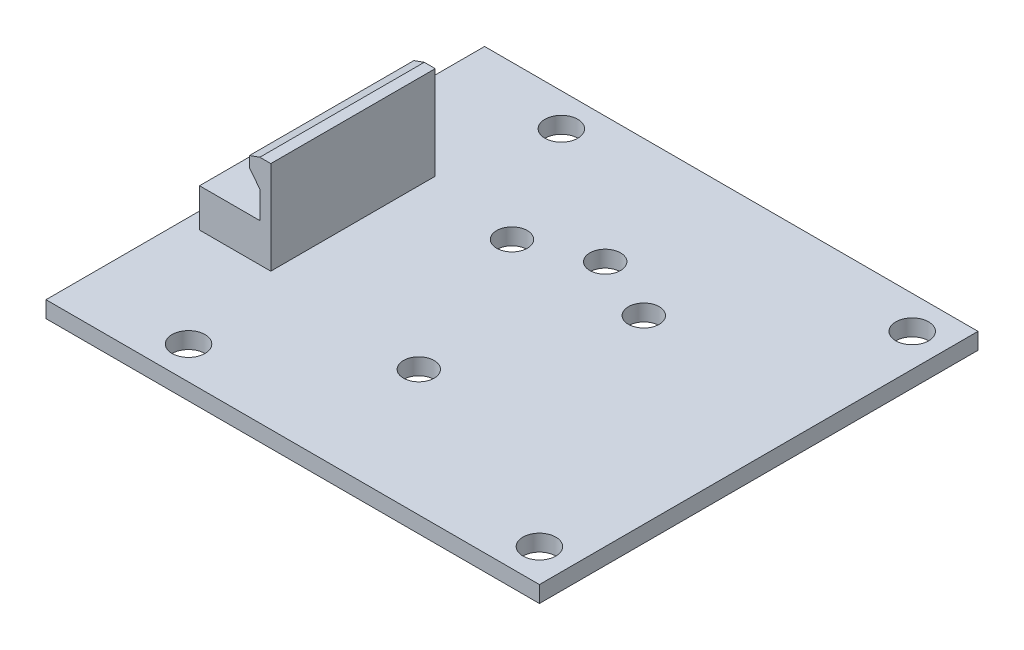
SolidWorks part; units mm, degrees
ref_plane "Front Plane" through (0, 0, 0) normal (0, 0, 1) x (1, 0, 0)
ref_plane "Top Plane" through (0, 0, 0) normal (0, 1, 0) x (1, 0, 0)
ref_plane "Right Plane" through (0, 0, 0) normal (1, 0, 0) x (0, 0, -1)
sketch "Sketch2" plane through (0, 0, 0) normal (0, 1, 0) x (1, 0, 0)
  line L1 (-22.5, 20) -> (22.5, 20)
  line L2 (-22.5, 20) -> (-22.5, -20)
  line L3 (-22.5, -20) -> (22.5, -20)
  line L4 (22.5, 20) -> (22.5, -20)
  line L5 (-22.5, 20) -> (22.5, -20) construction
  line L6 (-22.5, -20) -> (22.5, 20) construction
  point P0 (0, 0)
  dimension "D1" = 40
  dimension "D2" = 45
extrude "Boss-Extrude2" add sketch "Sketch2" against normal blind 1.5
sketch "Sketch4" plane through (0, 0, 0) normal (0, 1, 0) x (1, 0, 0)
  line L0 (0, 0) -> (0, 8.5) construction
  line L1 (0, 0) -> (6.0104, 6.0104) construction
  circle A0 centre (0, 0) radius 8.5 construction
  circle A1 centre (0, 8.5) radius 1.4
  circle A2 centre (6.0104, 6.0104) radius 1.4
  circle A3 centre (8.5, 0) radius 1.4 [skipped]
  circle A4 centre (6.0104, -6.0104) radius 1.4 [skipped]
  circle A5 centre (0, -8.5) radius 1.4
  circle A6 centre (-6.0104, -6.0104) radius 1.4 [skipped]
  circle A7 centre (-8.5, 0) radius 1.4 [skipped]
  circle A8 centre (-6.0104, 6.0104) radius 1.4
  dimension "D1" = 8
  dimension "D2" = 45
extrude "Cut-Extrude1" cut sketch "Sketch4" against normal through all
sketch "Sketch5" plane through (0, 0, 0) normal (0, 1, 0) x (1, 0, 0)
  line L0 (-22.5, 20) -> (-22.5, -20) construction
  line L1 (-21, -7.5) -> (-14.5, -7.5)
  line L2 (-21, -7.5) -> (-21, 7.5)
  line L3 (-21, 7.5) -> (-14.5, 7.5)
  line L4 (-14.5, -7.5) -> (-14.5, 7.5)
  line L5 (22.5, 20) -> (-22.5, 20) construction
  dimension "D1" = 15
  dimension "D2" = 1.5
  dimension "D3" = 6.5
  dimension "D4" = 12.5
extrude "Boss-Extrude3" add sketch "Sketch5" along normal blind 3.5
ref_plane "Plane1" through (0, 3.5, 0) normal (0, 1, 0) x (1, 0, 0)
sketch "Sketch6" plane through (0, 3.5, 0) normal (0, 1, 0) x (1, 0, 0)
  line L0 (-14.5, 7.5) -> (-21, 7.5) construction
  line L1 (-14.5, -7.5) -> (-15.5, -7.5)
  line L2 (-14.5, -7.5) -> (-14.5, 7.5)
  line L3 (-14.5, 7.5) -> (-15.5, 7.5)
  line L4 (-15.5, -7.5) -> (-15.5, 7.5)
  dimension "D1" = 1
extrude "Boss-Extrude4" add sketch "Sketch6" along normal blind 5
ref_plane "Plane2" through (0, 0, 7.5) normal (0, 0, 1) x (1, 0, 0)
sketch "Sketch7" plane through (0, 0, 7.5) normal (0, 0, 1) x (1, 0, 0)
  line L0 (-15.5, 8.5) -> (-16.4428, 8.1667)
  line L1 (-16.4428, 8.1667) -> (-16.4428, 7.1667)
  line L2 (-16.4428, 7.1667) -> (-15.5, 6)
  line L3 (-15.5, 8.5) -> (-15.5, 3.5) construction
  line L10 (-21, 0) -> (-14.5, 0)
  line L11 (-14.5, 0) -> (-14.5, 8.5)
  line L12 (-14.5, 8.5) -> (-15.5, 8.5)
  line L13 (-15.5, 8.5) -> (-15.5, 3.5)
  line L14 (-15.5, 3.5) -> (-21, 3.5)
  line L15 (-21, 3.5) -> (-21, 0)
  line L19 (-15.5, 8.5) -> (-15.5, 6)
  dimension "D1" = 1
  dimension "D2" = 1
  dimension "D3" = 1.5
  dimension "D4" = 0
extrude "Boss-Extrude5" add sketch "Sketch7" against normal blind 15
sketch "Sketch9" plane through (0, 0, 0) normal (0, 1, 0) x (1, 0, 0)
  line L0 (-22.5, 20) -> (-22.5, -20) construction
  line L1 (22.5, 20) -> (-22.5, 20) construction
  line L2 (-22.5, -20) -> (22.5, -20) construction
  line L3 (22.5, -20) -> (22.5, 20) construction
  circle A0 centre (-12.5, 17) radius 1.5
  circle A1 centre (-12.5, -17) radius 1.5
  circle A2 centre (19.5, 17) radius 1.5
  circle A3 centre (19.5, -17) radius 1.5
  dimension "D1" = 10
  dimension "D3" = 3
  dimension "D5" = 3
  dimension "D7" = 3
  dimension "D2" = 3
  dimension "D4" = 10
  dimension "D6" = 3
extrude "Cut-Extrude2" cut sketch "Sketch9" against normal through all
